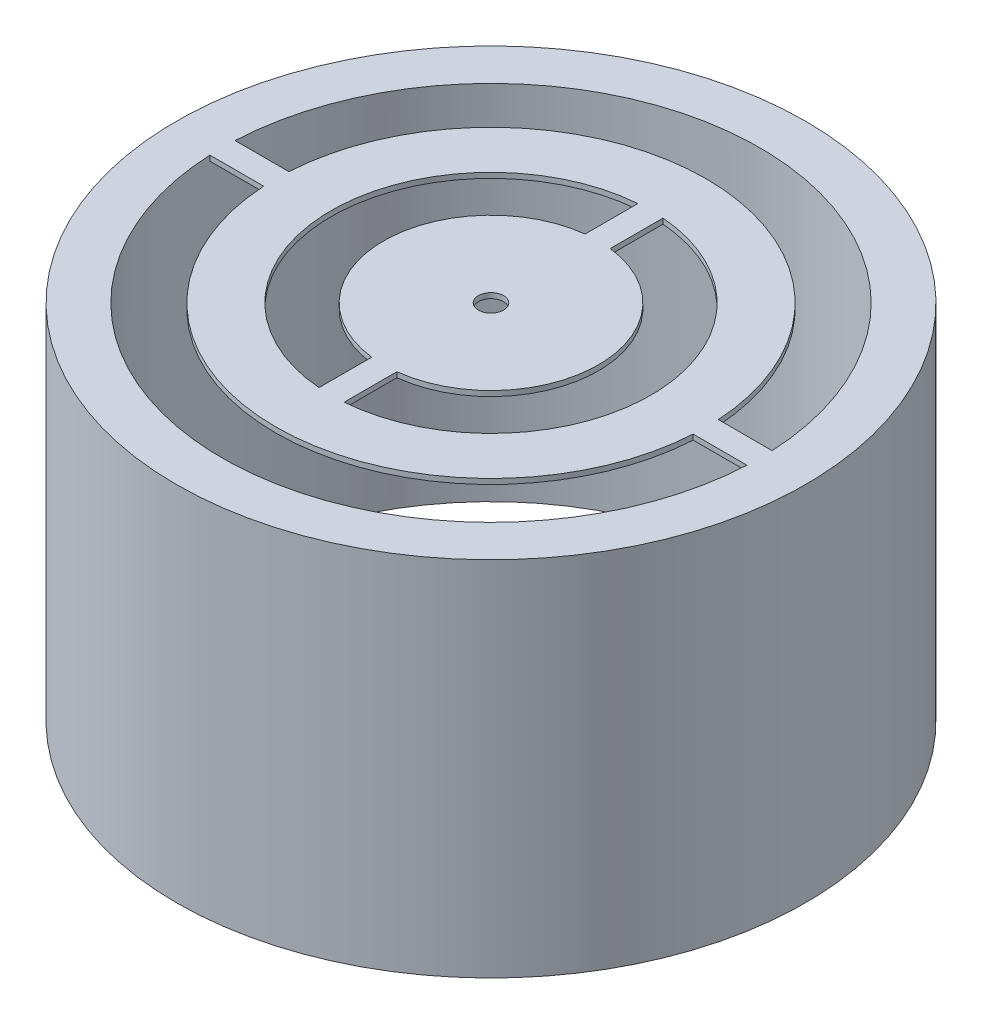
SolidWorks part; units mm, degrees
ref_plane "Front Plane" through (0, 0, 0) normal (0, 0, 1) x (1, 0, 0)
ref_plane "Top Plane" through (0, 0, 0) normal (0, 1, 0) x (1, 0, 0)
ref_plane "Right Plane" through (0, 0, 0) normal (1, 0, 0) x (0, 0, -1)
sketch "Sketch1" plane through (0, 0, 0) normal (0, 1, 0) x (1, 0, 0)
  line L0 (0, 0.6) -> (14.988, 0.6) construction
  line L1 (-12.8017, 0.6) -> (-10.2352, 0.6)
  line L2 (14.988, 0.6) -> (-14.988, 0.6) construction
  line L3 (10.2352, 0.6) -> (12.8017, 0.6)
  line L4 (-15, 0) -> (15, 0) construction
  line L5 (0.6, 0) -> (0.6, 14.988) construction
  line L6 (-0.6, 0) -> (-0.6, 14.988) construction
  line L7 (-0.6, 7.6002) -> (-0.6, 5.085)
  line L8 (0.6, 5.085) -> (0.6, 7.6002)
  line L9 (0.6, -5.085) -> (0.6, -7.6002)
  line L10 (-0.6, -7.6002) -> (-0.6, -5.085)
  line L11 (-12.8017, -0.6) -> (-10.2352, -0.6)
  line L12 (10.2352, -0.6) -> (12.8017, -0.6)
  circle A0 centre (0, 0) radius 15
  circle A5 centre (0, 0) radius 0.6
  arc A6 (-12.8017, 0.6) -> (12.8017, 0.6) centre (0, 0) cw
  arc A7 (-10.2352, 0.6) -> (10.2352, 0.6) centre (0, 0) cw
  arc A8 (-0.6, 7.6002) -> (-0.6, -7.6002) centre (0, 0) ccw
  arc A9 (0.6, 7.6002) -> (0.6, -7.6002) centre (0, 0) cw
  arc A10 (-0.6, 5.085) -> (-0.6, -5.085) centre (0, 0) ccw
  arc A11 (0.6, 5.085) -> (0.6, -5.085) centre (0, 0) cw
  arc A12 (-10.2352, -0.6) -> (10.2352, -0.6) centre (0, 0) ccw
  arc A13 (-12.8017, -0.6) -> (12.8017, -0.6) centre (0, 0) ccw
extrude "Boss-Extrude1" add sketch "Sketch1" along normal blind 0.25
sketch "Sketch2" plane through (0, 0.25, 0) normal (0, 1, 0) x (1, 0, 0)
  circle A0 centre (0, 0) radius 15
  circle A1 centre (0, 0) radius 12.8157
extrude "Boss-Extrude2" add sketch "Sketch2" against normal blind 17.268
